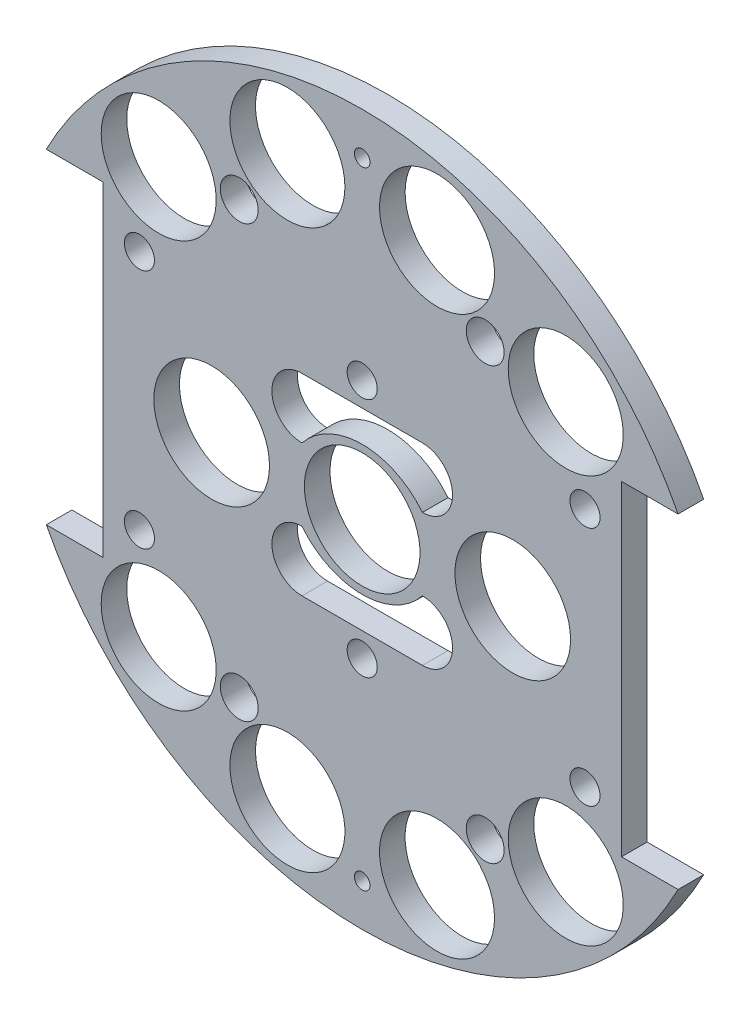
SolidWorks part; units mm, degrees
ref_plane "Front Plane" through (0, 0, 0) normal (0, 0, 1) x (1, 0, 0)
ref_plane "Top Plane" through (0, 0, 0) normal (0, 1, 0) x (1, 0, 0)
ref_plane "Right Plane" through (0, 0, 0) normal (1, 0, 0) x (0, 0, -1)
sketch "Sketch1" plane through (0, 0, 0) normal (0, 0, 1) x (1, 0, 0)
  line L0 (0, 0) -> (-82.1241, 0) construction
  line L1 (0, 0) -> (0, 95.6219) construction
  line L3 (-66.6236, 34.29) -> (-54.6856, 34.29)
  line L5 (-66.6236, -34.29) -> (-54.6856, -34.29)
  line L6 (-54.6856, 34.29) -> (-54.6856, -34.29)
  line L7 (66.6236, -34.29) -> (54.6856, -34.29)
  line L8 (66.6236, 34.29) -> (54.6856, 34.29)
  line L9 (54.6856, 34.29) -> (54.6856, -34.29)
  arc A0 (-66.6236, -34.29) -> (66.6236, -34.29) centre (0, 0) ccw
  circle A1 centre (-45.466, 11.049) radius 1.651
  circle A2 centre (-20.0673, 10.795) radius 1.651
  circle A3 centre (-20.0673, -10.795) radius 1.651
  circle A4 centre (-45.466, -11.049) radius 1.651
  circle A5 centre (45.466, -11.049) radius 1.651
  circle A6 centre (20.0673, -10.795) radius 1.651
  circle A7 centre (20.0673, 10.795) radius 1.651
  circle A8 centre (45.466, 11.049) radius 1.651
  arc A9 (66.6236, 34.29) -> (-66.6236, 34.29) centre (0, 0) ccw
  dimension "D2" = 3.302
  dimension "D3" = 3.302
  dimension "D4" = 25.4
  dimension "D5" = 10.795
  dimension "D10" = 45.466
  dimension "D6" = 68.58
  dimension "D7" = 11.938
  dimension "D8" = 74.93
  dimension "D9" = 74.93
  dimension "D11" = 34.29
extrude "Boss-Extrude2" add sketch "Sketch1" along normal blind 5.3975
sketch "Sketch4" plane through (0, 0, 0) normal (0, 0, -1) x (-1, 0, 0)
  line L1 (51.5324, -18.4451) -> (14.45, -18.4451)
  line L2 (51.5324, -18.4451) -> (51.5324, 15.6028)
  line L3 (51.5324, 15.6028) -> (14.45, 15.6028)
  line L4 (14.45, -18.4451) -> (14.45, 15.6028)
  line L5 (-15.5728, -16.8859) -> (-52.5974, -16.8859)
  line L6 (-15.5728, -16.8859) -> (-15.5728, 15.6028)
  line L7 (-15.5728, 15.6028) -> (-52.5974, 15.6028)
  line L8 (-52.5974, -16.8859) -> (-52.5974, 15.6028)
extrude "Boss-Extrude3" add sketch "Sketch4" against normal up to surface (5.3975 mm away) up to face at (18.4163, 10.795, 5.3975)
sketch "Sketch3" plane through (0, 0, 0) normal (0, 0, -1) x (-1, 0, 0)
  line L0 (0, 0) -> (0, -116.2908) construction
  line L1 (0, 0) -> (-153.8039, 0) construction
  line L2 (15.7776, -58.8828) -> (0, 0) construction
  arc A0 (-66.6236, -34.29) -> (66.6236, -34.29) centre (0, 0) ccw construction
  circle A2 centre (0, 0) radius 12.192
  circle A4 centre (-42.926, -42.926) radius 12.1285
  circle A6 centre (15.7776, -58.8828) radius 12.1285
  circle A7 centre (15.7776, 58.8828) radius 12.1285
  circle A8 centre (-42.926, 42.926) radius 12.1285
  circle A11 centre (42.926, 42.926) radius 12.1285
  circle A12 centre (-15.7776, 58.8828) radius 12.1285
  circle A13 centre (-15.7776, -58.8828) radius 12.1285
  circle A14 centre (42.926, -42.926) radius 12.1285
  point P36 (0, 0)
  point P53 (0, 0)
  point P55 (0, 0)
  dimension "D2" = 42.926
  dimension "D3" = 42.926
  dimension "D4" = 0
  dimension "D5" = 0
  dimension "D6" = 15
  dimension "D10" = 60.96
  dimension "D11" = 24.384
extrude "Cut-Extrude2" cut sketch "Sketch3" against normal through all
extrude "Cut-Extrude4" cut sketch "Sketch6" against normal through all both and the other way through all
sketch "Sketch6" plane through (31.3134, -132.614, 3.175) normal (0, 0, 1) x (0, -1, 0)
  line L0 (-132.614, -31.3134) -> (-132.614, 57.8454) construction
  line L1 (-132.614, -31.3134) -> (-222.516, -31.3134) construction
  circle A0 centre (-158.014, 14.4066) radius 3.175
  circle A1 centre (-173.254, -31.3134) radius 3.175
  circle A3 centre (-158.014, -77.0334) radius 3.175
  circle A4 centre (-107.214, -77.0334) radius 3.175
  circle A5 centre (-91.974, -31.3134) radius 3.175
  circle A6 centre (-107.214, 14.4066) radius 3.175
extrude "Cut-Extrude5" cut sketch "Sketch7" against normal blind 16.51
sketch "Sketch7" plane through (31.3134, -132.559, 15.875) normal (0, 0, 1) x (0, -1, 0)
  line L0 (-132.559, -31.3134) -> (-132.559, -98.8476) construction
  line L1 (-132.559, -31.3134) -> (-20.2053, -31.3134) construction
  circle A1 centre (-198.599, -31.3134) radius 1.651
  circle A2 centre (-66.519, -31.3134) radius 1.651
  circle A3 centre (-132.559, -82.1134) radius 1.651
  circle A4 centre (-132.559, 19.4866) radius 1.651
sketch "Sketch12" plane through (0, 0, 0) normal (0, 0, -1) x (-1, 0, 0)
  line L0 (0, 0) -> (0, 51.8011) construction
  circle A0 centre (25.9376, 45.466) radius 4
  circle A2 centre (15.7776, 58.8828) radius 12.1285 construction
  circle A3 centre (25.9376, -45.466) radius 4
  circle A5 centre (42.926, -42.926) radius 12.1285 construction
  circle A6 centre (-25.9376, 45.466) radius 4
  circle A7 centre (42.926, 42.926) radius 12.1285 construction
  circle A9 centre (-25.9376, -45.466) radius 4
  dimension "D1" = 8
  dimension "D3" = 10.16
  dimension "D4" = 8
  dimension "D5" = 0
  dimension "D6" = 2.54
  dimension "D2" = 2.54
extrude "Cut-Extrude10" cut sketch "Sketch12" against normal blind 83.312
sketch "Sketch15" plane through (0, 0, 0) normal (0, 0, -1) x (-1, 0, 0)
  line L0 (0, 0) -> (91.4732, 0) construction
  circle A0 centre (0, 66.04) radius 1.651
  circle A1 centre (0, -66.04) radius 1.651
  dimension "D1" = 3.302
  dimension "D2" = 66.04
extrude "Cut-Extrude17" cut sketch "Sketch15" against normal blind 83.312
extrude "Cut-Extrude37" cut sketch "Sketch35" against normal blind 48.768 and the other way blind 103.378
sketch "Sketch35" plane through (-30.092, 4.0835, -42.4815) normal (0, 0, 1) x (1, 0, 0)
  line L0 (30.092, -4.0835) -> (148.6336, -4.0835) construction
  line L1 (30.092, -4.0835) -> (30.092, 90.452) construction
  circle A0 centre (-16.898, 21.3165) radius 3.175
  circle A1 centre (77.082, 21.3165) radius 3.175
  circle A2 centre (30.092, 21.3165) radius 3.175
  circle A4 centre (77.082, -29.4835) radius 3.175
  circle A5 centre (30.092, -29.4835) radius 3.175
  circle A6 centre (-16.898, -29.4835) radius 3.175
sketch "Sketch40" plane through (0, 0, 0) normal (0, 0, -1) x (-1, 0, 0)
  line L0 (12.7, -20.32) -> (-12.7, -20.32)
  line L1 (0, 0) -> (-37.8831, 0) construction
  line L2 (12.7, 20.32) -> (-12.7, 20.32)
  arc A0 (12.7, -20.32) -> (12.7, -7.62) centre (12.7, -13.97) ccw
  arc A1 (-12.7, -7.62) -> (-12.7, -20.32) centre (-12.7, -13.97) ccw
  arc A2 (12.7, -7.62) -> (-12.7, -7.62) centre (0, 2.54) cw
  arc A3 (-12.7, 7.62) -> (-12.7, 20.32) centre (-12.7, 13.97) cw
  arc A4 (12.7, 7.62) -> (-12.7, 7.62) centre (0, -2.54) ccw
  arc A5 (12.7, 20.32) -> (12.7, 7.62) centre (12.7, 13.97) cw
  circle A6 centre (-31.75, 0) radius 12.192
  circle A7 centre (31.75, 0) radius 12.192
  dimension "D1" = 12.7
  dimension "D2" = 12.7
  dimension "D7" = 24.384
  dimension "D8" = 24.384
  dimension "D3" = 13.97
  dimension "D4" = 2.54
  dimension "D5" = 25.4
  dimension "D6" = 12.7
  dimension "D9" = 63.5
  dimension "D10" = 31.75
extrude "Cut-Extrude43" cut sketch "Sketch40" against normal blind 25.4
